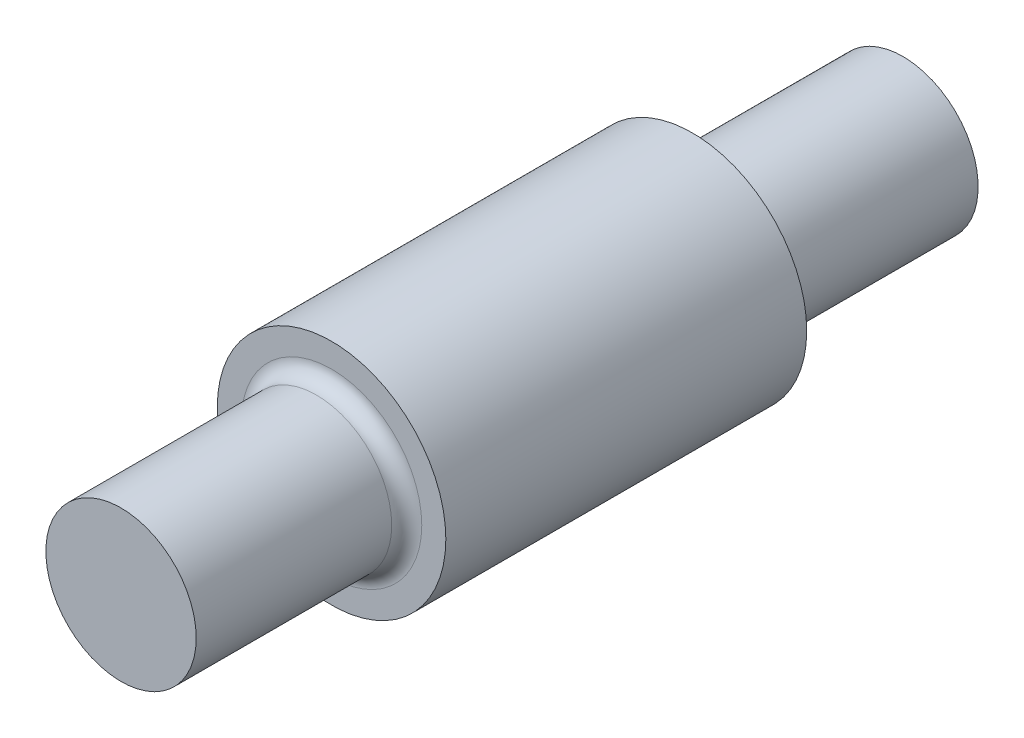
SolidWorks part; units mm, degrees
ref_plane "Front Plane" through (0, 0, 0) normal (0, 0, 1) x (1, 0, 0)
ref_plane "Top Plane" through (0, 0, 0) normal (0, 1, 0) x (1, 0, 0)
ref_plane "Right Plane" through (0, 0, 0) normal (1, 0, 0) x (0, 0, -1)
sketch "Sketch1" plane through (0, 0, 0) normal (0, 0, 1) x (1, 0, 0)
  circle A0 centre (0, 0) radius 19
  dimension "D1" = 38
extrude "Boss-Extrude1" add sketch "Sketch1" along normal blind 130
sketch "Sketch2" plane through (0, 0, 130) normal (0, 0, 1) x (1, 0, 0)
  circle A0 centre (0, 0) radius 12.5
  circle A1 centre (0, 0) radius 19
  dimension "D1" = 25
  dimension "D2" = 38
extrude "Cut-Extrude2" cut sketch "Sketch2" against normal blind 35 contours A1 | A0
sketch "Sketch3" plane through (0, 0, 0) normal (0, 0, -1) x (-1, 0, 0)
  circle A0 centre (0, 0) radius 12.5
  circle A1 centre (0, 0) radius 19
  dimension "D1" = 25
  dimension "D2" = 38
extrude "Cut-Extrude3" cut sketch "Sketch3" against normal blind 35 contours A1 | A0
fillet "Fillet1" radius 2.5 2 edges at (12.5, 0, 95) (-12.5, 0, 35)
